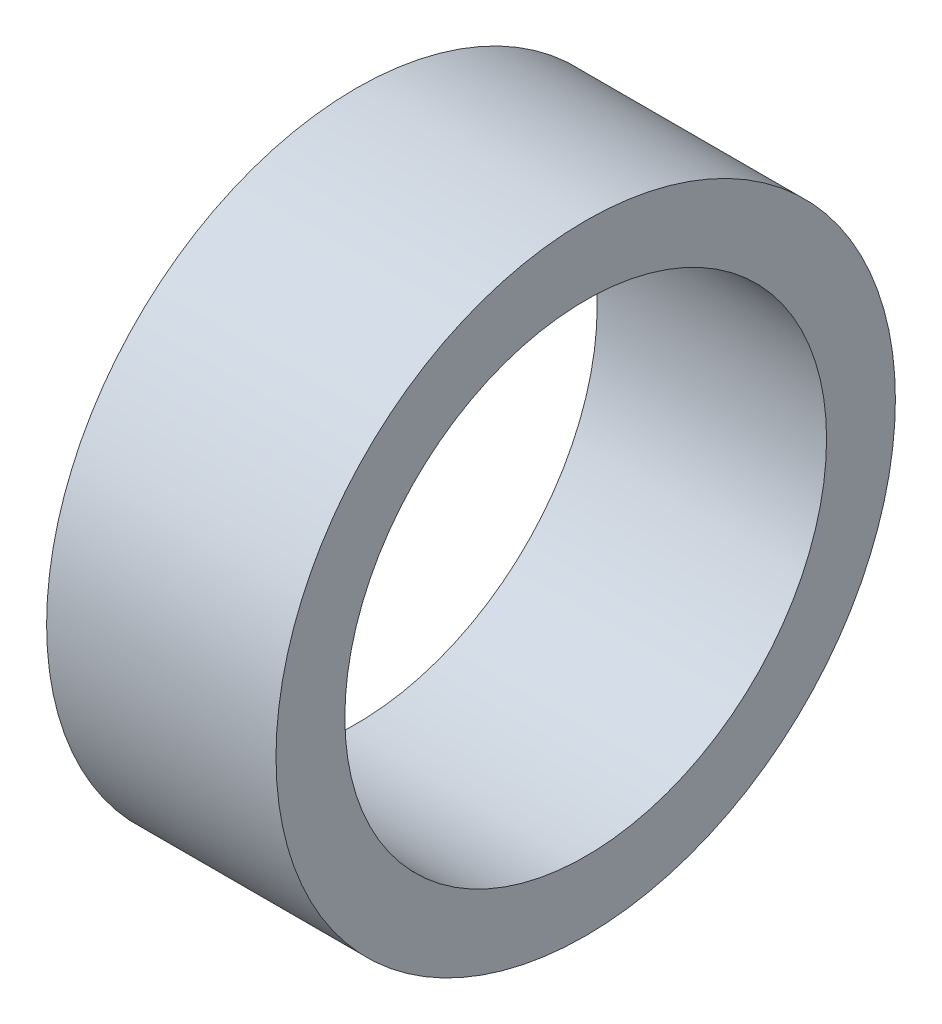
SolidWorks part; units mm, degrees
ref_plane "Спереди" through (0, 0, 0) normal (0, 0, 1) x (1, 0, 0)
ref_plane "Сверху" through (0, 0, 0) normal (0, 1, 0) x (1, 0, 0)
ref_plane "Справа" through (0, 0, 0) normal (1, 0, 0) x (0, 0, -1)
sketch "Эскиз1" plane through (0, 0, 0) normal (1, 0, 0) x (0, 0, -1)
  circle A0 centre (0, 0) radius 5.25
  circle A1 centre (0, 0) radius 6.75
  dimension "D1" = 10.5
  dimension "D2" = 13.5
extrude "Бобышка-Вытянуть1" add sketch "Эскиз1" along normal blind 5
